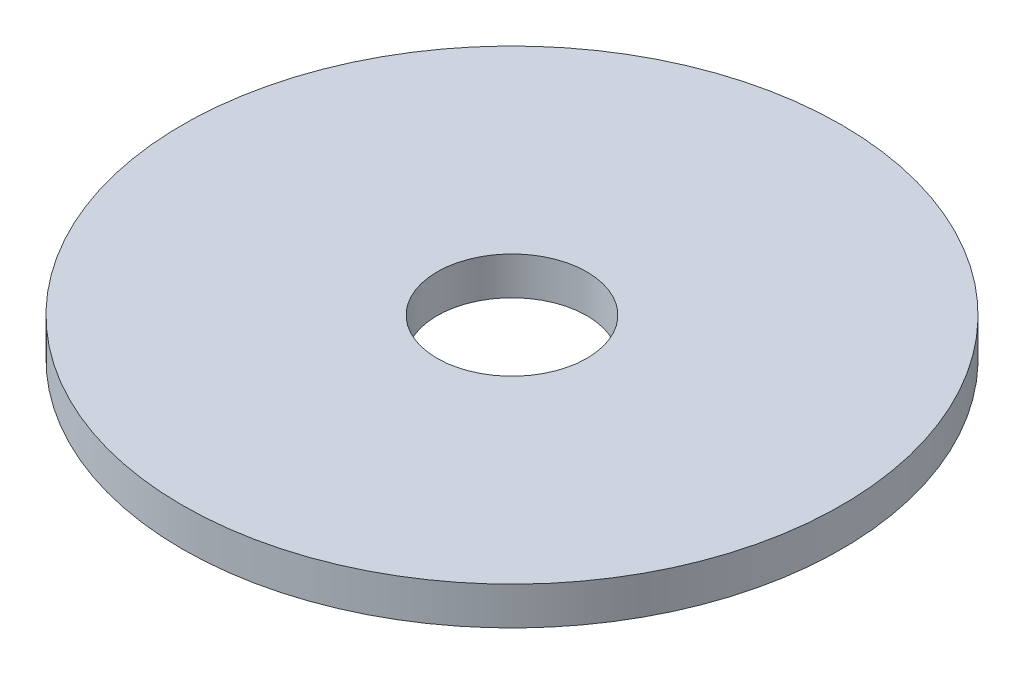
SolidWorks part; units mm, degrees
material "6061-T6 (SS)"
ref_plane "Front Plane" through (0, 0, 0) normal (0, 0, 1) x (1, 0, 0)
ref_plane "Top Plane" through (0, 0, 0) normal (0, 1, 0) x (1, 0, 0)
ref_plane "Right Plane" through (0, 0, 0) normal (1, 0, 0) x (0, 0, -1)
sketch "Sketch1" plane through (0, 0, 0) normal (0, 1, 0) x (1, 0, 0)
  circle A0 centre (0, 0) radius 83.82
  dimension "D1" = 167.64
extrude "Boss-Extrude1" add sketch "Sketch1" along normal mid plane 9.652
sketch "Sketch2" plane through (0, -4.826, 0) normal (0, -1, 0) x (1, 0, 0)
  circle A0 centre (0, 0) radius 19.05
  dimension "D1" = 38.1
extrude "Cut-Extrude1" cut sketch "Sketch2" against normal up to surface (9.652 mm away) up to face at (0, 4.826, 83.82)
